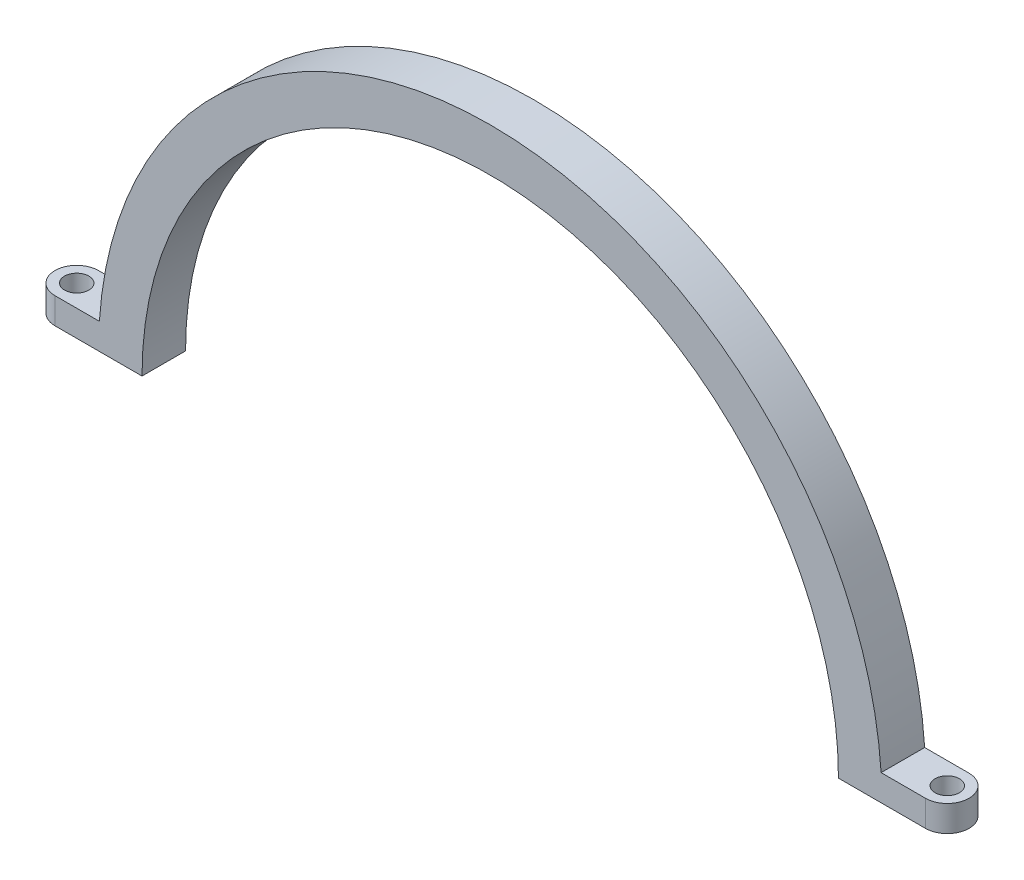
SolidWorks part; units mm, degrees
ref_plane "前视基准面" through (0, 0, 0) normal (0, 0, 1) x (1, 0, 0)
ref_plane "上视基准面" through (0, 0, 0) normal (0, 1, 0) x (1, 0, 0)
ref_plane "右视基准面" through (0, 0, 0) normal (1, 0, 0) x (0, 0, -1)
other "Configuration Table"
sketch "草图1" plane through (0, 0, 0) normal (0, 0, 1) x (1, 0, 0)
  line L0 (-45, 0) -> (-40, 0)
  line L1 (40, 0) -> (45, 0)
  arc A0 (45, 0) -> (-45, 0) centre (0, 0) ccw
  arc A1 (40, 0) -> (-40, 0) centre (0, 0) ccw
  dimension "D1" = 90
  dimension "D2" = 80
extrude "凸台-拉伸1" add sketch "草图1" along normal blind 5
sketch "草图2" plane through (0, 0, 0) normal (0, -1, 0) x (1, 0, 0)
  line L1 (-45, 5) -> (-50, 5)
  line L3 (-45, 0) -> (-50, 0)
  line L5 (-45, 5) -> (-44.1323, 5)
  line L7 (-45, 0) -> (-44.1323, 0)
  line L8 (-44.1323, 5) -> (-44.1323, 0)
  line L10 (0, -1000) -> (0, 49000) construction
  line L11 (-40, 0) -> (40, 0) construction
  line L12 (44.1323, 5) -> (44.1323, 0)
  line L13 (45, 0) -> (44.1323, 0)
  line L14 (45, 5) -> (44.1323, 5)
  line L15 (45, 0) -> (50, 0)
  line L16 (45, 5) -> (50, 5)
  arc A0 (-50, 5) -> (-50, 0) centre (-50, 2.5) ccw
  circle A1 centre (-50, 2.5) radius 1.4
  arc A2 (50, 5) -> (50, 0) centre (50, 2.5) cw
  circle A3 centre (50, 2.5) radius 1.4
  point P14 (0, 0)
  dimension "D3" = 5
  dimension "D1" = 2.8
  dimension "D4" = 2.8
  dimension "D2" = 5
extrude "凸台-拉伸2" add sketch "草图2" against normal blind 3
